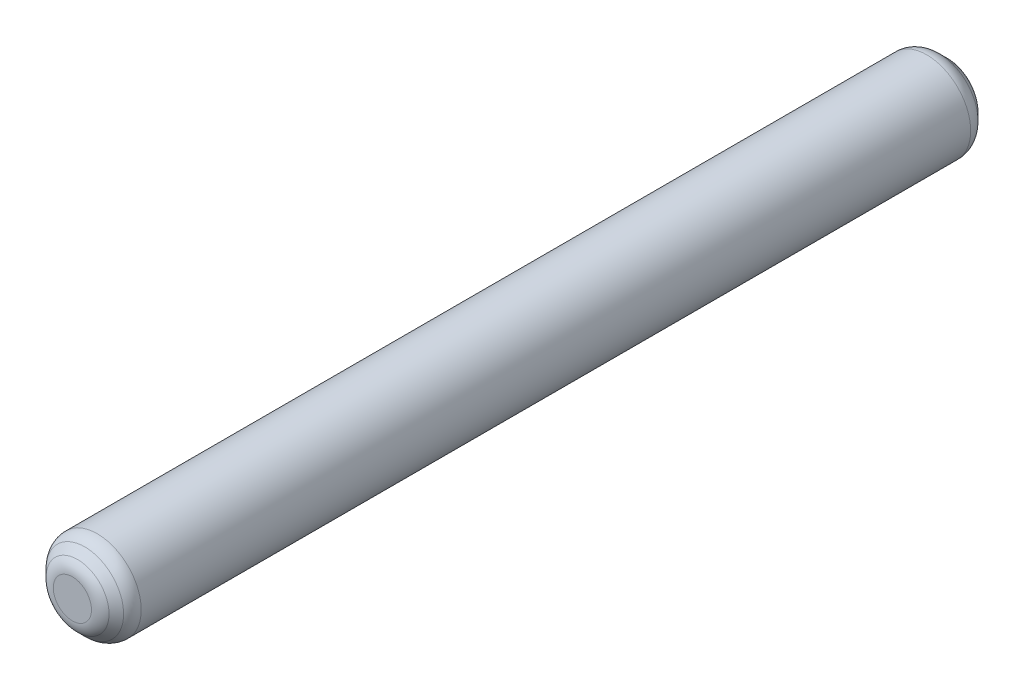
SolidWorks part; units mm, degrees
ref_plane "Front" through (0, 0, 0) normal (0, 0, 1) x (1, 0, 0)
ref_plane "Top" through (0, 0, 0) normal (0, 1, 0) x (1, 0, 0)
ref_plane "Right" through (0, 0, 0) normal (1, 0, 0) x (0, 0, -1)
sketch "Sketch2" plane through (0, 0, 0) normal (0, 0, 1) x (1, 0, 0)
  circle A0 centre (0, 0) radius 0.5
extrude "Boss-Extrude1" add sketch "Sketch2" along normal blind 10
chamfer "Chamfer1" distance 0.2 angle 45 2 edges at (0.5, 0, 0) (0.5, 0, 10)
fillet "Fillet1" radius 0.2 1 edges at (0.5, 0, 0.2)
fillet "Fillet2" radius 0.2 1 edges at (0.3, 0, 0)
fillet "Fillet3" radius 0.2 2 edges at (0.3, 0, 10) (0.5, 0, 9.8)
